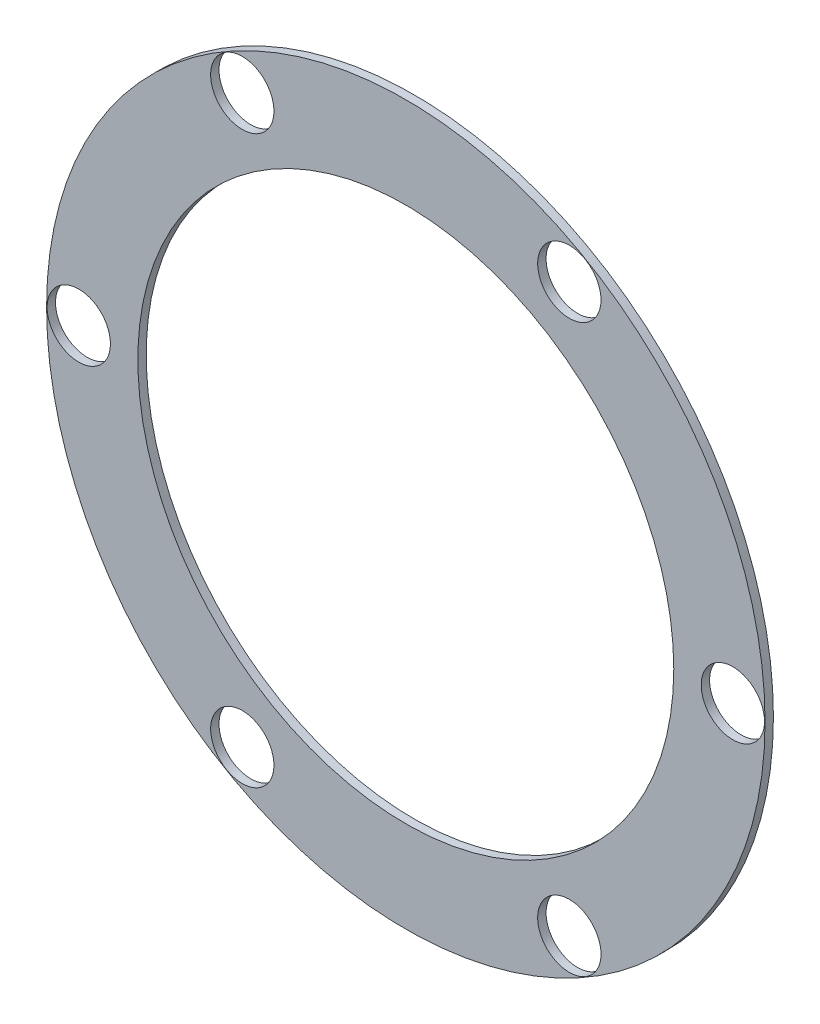
SolidWorks part; units mm, degrees
material "BUTYL"
ref_plane "Front Plane" through (0, 0, 0) normal (0, 0, 1) x (1, 0, 0)
ref_plane "Top Plane" through (0, 0, 0) normal (0, 1, 0) x (1, 0, 0)
ref_plane "Right Plane" through (0, 0, 0) normal (1, 0, 0) x (0, 0, -1)
sketch "Sketch1" plane through (0, 0, 0) normal (0, 0, 1) x (1, 0, 0)
  arc A0 (-15.4505, 7.0909) -> (-15.4505, -7.0909) centre (0, 0) ccw construction
  circle A1 centre (-15.5, 0) radius 1.5
  circle A2 centre (-7.75, 13.4234) radius 1.5
  circle A3 centre (7.75, 13.4234) radius 1.5
  circle A4 centre (15.5, 0) radius 1.5
  circle A5 centre (7.75, -13.4234) radius 1.5
  circle A6 centre (-7.75, -13.4234) radius 1.5
  arc A7 (-15.4735, 7.1025) -> (-15.4735, -7.1025) centre (0, 0) ccw
  arc A8 (-11.7048, 4.9283) -> (-11.7048, -4.9283) centre (0, 0) ccw
  arc A10 (1.5844, 16.926) -> (1.5858, 16.9517) centre (0, 17.0257) ccw
  arc A12 (13.8877, 9.8492) -> (13.8662, 9.8351) centre (14.7447, 8.5128) ccw
  arc A14 (13.8662, -9.8351) -> (13.8877, -9.8492) centre (14.7447, -8.5128) ccw
  arc A16 (1.5858, -16.9517) -> (1.5844, -16.926) centre (0, -17.0257) ccw
  arc A18 (-15.4505, -7.0909) -> (-15.4735, -7.1025) centre (-14.7447, -8.5128) ccw
  arc A20 (-13.8662, 9.8351) -> (-13.8877, 9.8492) centre (-14.7447, 8.5128) ccw
  arc A22 (-1.5844, 12.6008) -> (-10.1204, 7.6725) centre (0, 0) ccw
  arc A23 (-1.5858, 16.9517) -> (-13.8877, 9.8492) centre (0, 0) ccw
  arc A24 (-1.5844, 16.926) -> (-13.8662, 9.8351) centre (0, 0) ccw construction
  arc A25 (13.8877, 9.8492) -> (1.5858, 16.9517) centre (0, 0) ccw
  arc A26 (13.8662, 9.8351) -> (1.5844, 16.926) centre (0, 0) ccw construction
  arc A27 (10.1204, 7.6725) -> (1.5844, 12.6008) centre (0, 0) ccw
  arc A28 (11.7048, -4.9283) -> (11.7048, 4.9283) centre (0, 0) ccw
  arc A29 (15.4505, -7.0909) -> (15.4505, 7.0909) centre (0, 0) ccw construction
  arc A30 (15.4735, -7.1025) -> (15.4735, 7.1025) centre (0, 0) ccw
  arc A31 (-13.8662, -9.8351) -> (-1.5844, -16.926) centre (0, 0) ccw construction
  arc A32 (-13.8877, -9.8492) -> (-1.5858, -16.9517) centre (0, 0) ccw
  arc A33 (-10.1204, -7.6725) -> (-1.5844, -12.6008) centre (0, 0) ccw
  arc A34 (1.5844, -12.6008) -> (10.1204, -7.6725) centre (0, 0) ccw
  arc A35 (1.5844, -16.926) -> (13.8662, -9.8351) centre (0, 0) ccw construction
  arc A36 (1.5858, -16.9517) -> (13.8877, -9.8492) centre (0, 0) ccw
  arc A37 (-1.5858, 16.9517) -> (-1.5844, 16.926) centre (0, 17.0257) ccw
  arc A38 (15.4505, 7.0909) -> (15.4735, 7.1025) centre (14.7447, 8.5128) ccw
  arc A39 (15.4735, -7.1025) -> (15.4505, -7.0909) centre (14.7447, -8.5128) ccw
  arc A40 (-1.5844, -16.926) -> (-1.5858, -16.9517) centre (0, -17.0257) ccw
  arc A41 (-13.8877, -9.8492) -> (-13.8662, -9.8351) centre (-14.7447, -8.5128) ccw
  arc A42 (-15.4735, 7.1025) -> (-15.4505, 7.0909) centre (-14.7447, 8.5128) ccw
  circle A43 centre (0, 0) radius 17.0257
  circle A44 centre (0, 0) radius 12.7
  dimension "D1" = 3
  dimension "D2" = 34
  dimension "D4" = 25.4
  dimension "D7" = 3.175
  dimension "D8" = 34.0514
  dimension "D3" = 6
  dimension "D9" = 6
extrude "Boss-Extrude1" add sketch "Sketch1" along normal blind 0.3969 contours A0 A6 A5 A4 A3 A2 A1
